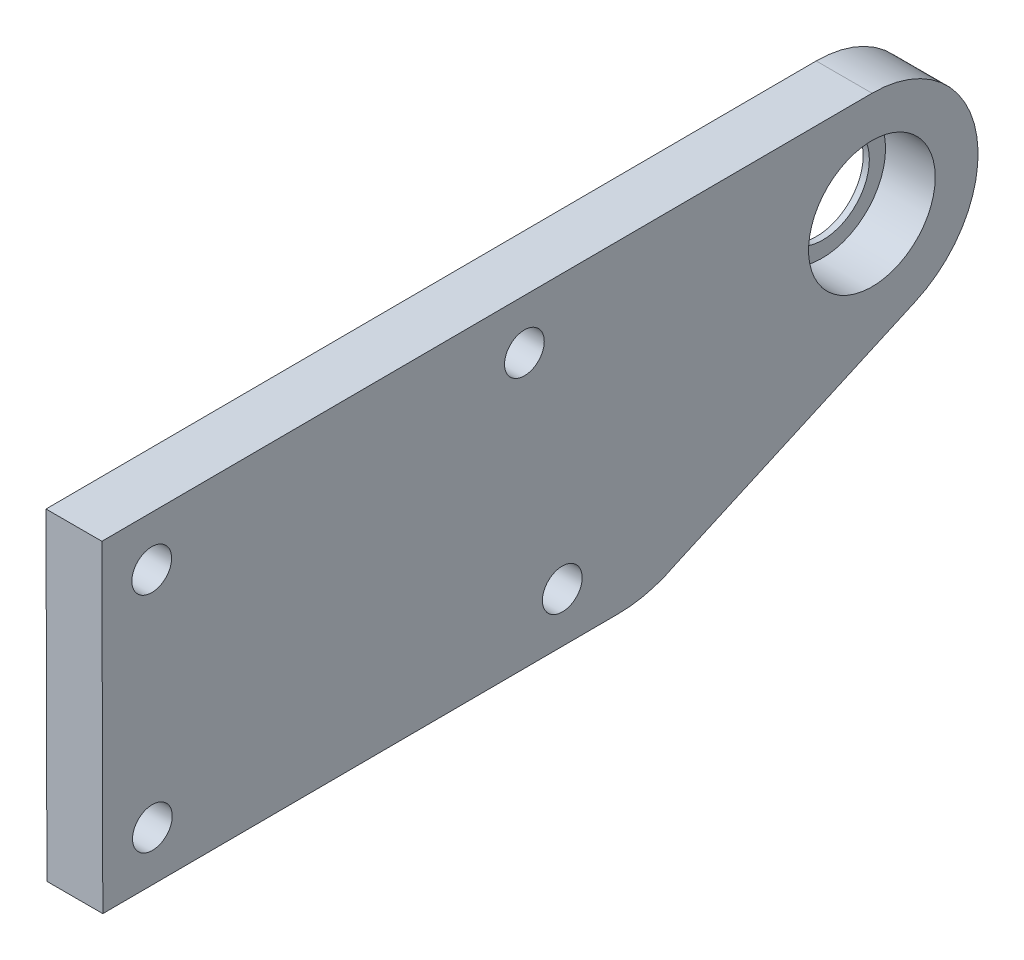
SolidWorks part; units mm, degrees
ref_plane "前视基准面" through (0, 0, 0) normal (0, 0, 1) x (1, 0, 0)
ref_plane "上视基准面" through (0, 0, 0) normal (0, 1, 0) x (1, 0, 0)
ref_plane "右视基准面" through (0, 0, 0) normal (1, 0, 0) x (0, 0, -1)
sketch "草图1" plane through (0, 0, 0) normal (1, 0, 0) x (0, 0, -1)
  line L1 (-15.7977, -16.5375) -> (3.4886, -7.8787)
  line L47 (-61.9105, -17.8437) -> (-20.4108, -17.685)
  line L49 (-61.9852, 8.1562) -> (-61.9105, -17.8437)
  line L50 (-61.9852, 8.1562) -> (0.0144, 8.3932)
  circle A0 centre (0.0469, -0.1067) radius 3.75
  arc A1 (3.4886, -7.8787) -> (0.0144, 8.3932) centre (0.0469, -0.1067) ccw
  circle A166 centre (-57.9737, 4.1715) radius 1.6
  circle A170 centre (-24.9222, -13.7023) radius 1.6
  circle A171 centre (-27.9739, 4.2862) radius 1.6
  circle A175 centre (-57.922, -13.8284) radius 1.6
  arc A176 (-20.4108, -17.685) -> (-15.7977, -16.5375) centre (-20.449, -7.6851) ccw
  point P0 (-150, 0)
  point P1 (135, 0)
  point P9 (-344.9533, 138.7825)
  point P10 (187.1329, 101.1747)
  point P11 (165.9429, -19)
  point P12 (-156.9154, -19)
  dimension "D7" = 4
  dimension "D8" = 22
  dimension "D9" = 7.5
  dimension "D10" = 8.5
  dimension "D4" = 4
  dimension "D11" = 62
  dimension "D12" = 41.5
  dimension "D13" = 26
  dimension "D6" = 33
  dimension "D5" = 4
  dimension "D2" = 18
  dimension "D1" = 30
  dimension "D3" = 4
extrude "凸台-拉伸1" add sketch "草图1" along normal blind 4.5
sketch "草图2" plane through (4.5, 0, 0) normal (1, 0, 0) x (0, 0, -1)
  circle A0 centre (0, 0) radius 5.1
  dimension "D1" = 10.2
extrude "切除-拉伸1" cut sketch "草图2" against normal blind 4
